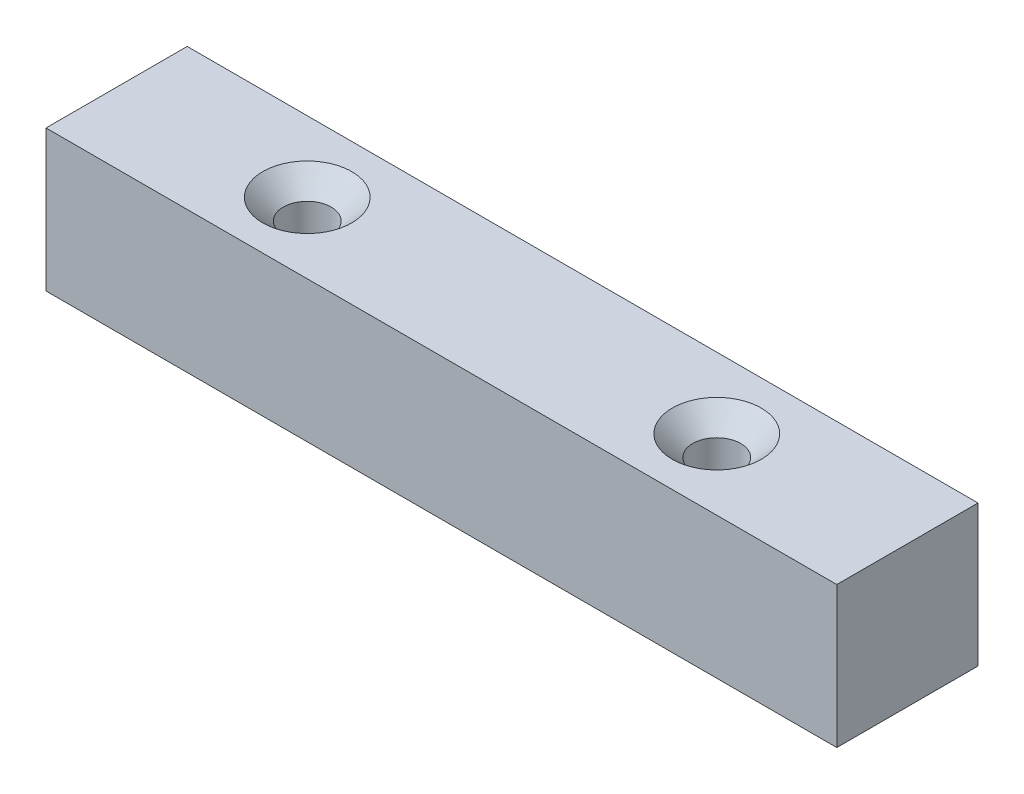
SolidWorks part; units mm, degrees
ref_plane "Front Plane" through (0, 0, 0) normal (0, 0, 1) x (1, 0, 0)
ref_plane "Top Plane" through (0, 0, 0) normal (0, 1, 0) x (1, 0, 0)
ref_plane "Right Plane" through (0, 0, 0) normal (1, 0, 0) x (0, 0, -1)
sketch "Sketch1" plane through (0, 0, 0) normal (0, 1, 0) x (1, 0, 0)
  line L1 (-27.4573, 16.4223) -> (28.5427, 16.4223)
  line L2 (-27.4573, 16.4223) -> (-27.4573, 6.4223)
  line L3 (-27.4573, 6.4223) -> (28.5427, 6.4223)
  line L4 (28.5427, 16.4223) -> (28.5427, 6.4223)
  dimension "D1" = 56
  dimension "D2" = 10
extrude "Boss-Extrude1" add sketch "Sketch1" along normal blind 10
hole_wizard "CSK for M3 Flat Head Machine Screw1" positions "Sketch4" profile "Sketch5" countersink size "M3" standard "ANSI Metric" end condition through all
sketch "Sketch4" plane through (0, 10, 0) normal (0, 1, 0) x (1, 0, 0)
  line L0 (-27.4573, 16.4223) -> (-27.4573, 6.4223) construction
  line L1 (28.5427, 6.4223) -> (28.5427, 16.4223) construction
  line L3 (-27.4573, 6.4223) -> (28.5427, 6.4223) construction
  point P0 (15.0427, 11.4223)
  point P2 (-13.9573, 11.4223)
  point P13 (15.0427, 11.1474)
  point P16 (0, 0)
  dimension "D1" = 13.5
  dimension "D2" = 13.5
  dimension "D3" = 5
  dimension "D4" = 5
sketch "Sketch5" plane through (15.0427, 10, -11.4223) normal (1, 0, 0) x (0, 0, 1)
  line L0 (0, 0) -> (0, 10)
  line L1 (0, 10) -> (1.7, 10)
  line L2 (1.7, 10) -> (1.7, 1.45)
  line L3 (1.7, 1.45) -> (3.15, 0)
  line L5 (3.15, 0) -> (0, 0)
  line L6 (-1.7, 1.45) -> (-3.15, 0) construction
  line L11 (0, -6.35) -> (0, 107.95) construction
  dimension "Thru Hole Dia." = 3.4
  dimension "Thru Hole Depth" = 10
  dimension "Near C'Sink Dia." = 6.3
  dimension "Near C'Sink Angle" = 90
hole_wizard "Ø5.0mm Dowel Hole1" positions "Sketch6" profile "Sketch7" hole size "Ø5.0" standard "ANSI Metric"
sketch "Sketch6" plane through (0, 0, 0) normal (0, -1, 0) x (-1, 0, 0)
  line L0 (27.4573, 16.4223) -> (27.4573, 6.4223) construction
  line L1 (-28.5427, 6.4223) -> (-28.5427, 16.4223) construction
  line L2 (27.4573, 6.4223) -> (-28.5427, 6.4223) construction
  point P0 (22.4573, 11.4223)
  point P2 (-23.5427, 11.4223)
  dimension "D1" = 5
  dimension "D2" = 5
  dimension "D3" = 5
  dimension "D4" = 5
sketch "Sketch7" plane through (-22.4573, 0, -11.4223) normal (1, 0, 0) x (0, 0, -1)
  line L0 (0, 0) -> (0, 6.5022)
  line L1 (0, 6.5022) -> (2.5, 5)
  line L2 (2.5, 5) -> (2.5, 0)
  line L5 (2.5, 0) -> (0, 0)
  line L10 (0, 6.5022) -> (-2.5, 5) construction
  line L11 (0, -6.35) -> (0, 107.95) construction
  dimension "Hole Dia." = 5
  dimension "Hole Depth" = 5
  dimension "Drill Angle" = 118
